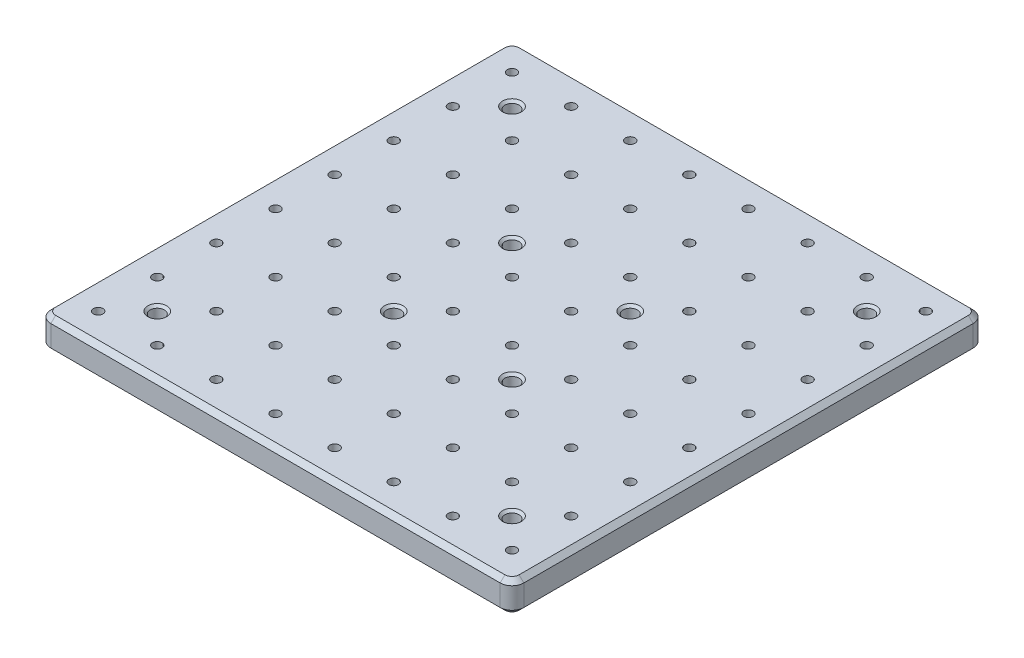
SolidWorks part; units mm, degrees
material "1023 碳钢板 (SS)"
ref_plane "前视基准面" through (0, 0, 0) normal (0, 0, 1) x (1, 0, 0)
ref_plane "上视基准面" through (0, 0, 0) normal (0, 1, 0) x (1, 0, 0)
ref_plane "右视基准面" through (0, 0, 0) normal (1, 0, 0) x (0, 0, -1)
sketch "草图1" plane through (0, 0, 0) normal (0, 1, 0) x (1, 0, 0)
  line L0 (0, 0) -> (0, 125.9326) construction
  line L1 (95, 100) -> (-95, 100)
  line L2 (100, 95) -> (100, -95)
  line L3 (95, -100) -> (-95, -100)
  line L4 (-100, 95) -> (-100, -95)
  line L5 (100, 100) -> (-100, -100) construction
  line L6 (100, -100) -> (-100, 100) construction
  line L7 (25, 25) -> (-25, 25) construction
  line L8 (25, 25) -> (25, -25) construction
  line L9 (25, -25) -> (-25, -25) construction
  line L10 (-25, 25) -> (-25, -25) construction
  line L11 (25, 25) -> (-25, -25) construction
  line L12 (25, -25) -> (-25, 25) construction
  line L13 (-37.5, 37.5) -> (-12.5, 37.5) construction
  line L14 (-37.5, 37.5) -> (-37.5, 12.5) construction
  line L15 (-37.5, 12.5) -> (-12.5, 12.5) construction
  line L16 (-12.5, 37.5) -> (-12.5, 12.5) construction
  line L17 (-37.5, 37.5) -> (-12.5, 12.5) construction
  line L18 (-37.5, 12.5) -> (-12.5, 37.5) construction
  line L20 (75, 75) -> (-75, 75) construction
  line L25 (75, 75) -> (75, -75) construction
  line L26 (75, -75) -> (-75, -75) construction
  line L27 (25, 75) -> (-25, 25) construction
  line L28 (25, 25) -> (-25, 75) construction
  line L29 (-37.5, 62.5) -> (-12.5, 87.5) construction
  line L30 (-37.5, 87.5) -> (-12.5, 62.5) construction
  line L31 (-37.5, 87.5) -> (-37.5, 62.5) construction
  line L32 (-37.5, 62.5) -> (-12.5, 62.5) construction
  line L33 (-12.5, 87.5) -> (-12.5, 62.5) construction
  line L34 (-37.5, 87.5) -> (-12.5, 87.5) construction
  line L35 (-75, 75) -> (-75, -75) construction
  line L36 (75, 75) -> (-75, -75) construction
  line L37 (75, -75) -> (-75, 75) construction
  circle A1 centre (-25, 25) radius 3
  circle A2 centre (25, 25) radius 3
  circle A3 centre (-25, -25) radius 3
  circle A4 centre (25, -25) radius 3
  circle A5 centre (-37.5, 37.5) radius 2
  circle A6 centre (-12.5, 37.5) radius 2
  circle A7 centre (-12.5, 12.5) radius 2
  circle A8 centre (-37.5, 12.5) radius 2
  circle A9 centre (37.5, 37.5) radius 2
  circle A10 centre (37.5, 12.5) radius 2
  circle A11 centre (12.5, 12.5) radius 2
  circle A12 centre (12.5, 37.5) radius 2
  circle A13 centre (87.5, 37.5) radius 2
  circle A14 centre (87.5, 12.5) radius 2
  circle A15 centre (62.5, 12.5) radius 2
  circle A16 centre (62.5, 37.5) radius 2
  circle A17 centre (-87.5, 37.5) radius 2
  circle A18 centre (-62.5, 37.5) radius 2
  circle A19 centre (-62.5, 12.5) radius 2
  circle A20 centre (-87.5, 12.5) radius 2
  circle A21 centre (-37.5, 87.5) radius 2
  circle A22 centre (-12.5, 87.5) radius 2
  circle A23 centre (-12.5, 62.5) radius 2
  circle A24 centre (-37.5, 62.5) radius 2
  circle A25 centre (37.5, 87.5) radius 2
  circle A26 centre (37.5, 62.5) radius 2
  circle A27 centre (12.5, 62.5) radius 2
  circle A28 centre (12.5, 87.5) radius 2
  circle A29 centre (87.5, 87.5) radius 2
  circle A30 centre (87.5, 62.5) radius 2
  circle A31 centre (62.5, 62.5) radius 2
  circle A32 centre (62.5, 87.5) radius 2
  circle A33 centre (-87.5, 87.5) radius 2
  circle A34 centre (-62.5, 87.5) radius 2
  circle A35 centre (-62.5, 62.5) radius 2
  circle A36 centre (-87.5, 62.5) radius 2
  circle A37 centre (-37.5, -12.5) radius 2
  circle A38 centre (-12.5, -12.5) radius 2
  circle A39 centre (-12.5, -37.5) radius 2
  circle A40 centre (-37.5, -37.5) radius 2
  circle A41 centre (37.5, -12.5) radius 2
  circle A42 centre (37.5, -37.5) radius 2
  circle A43 centre (12.5, -37.5) radius 2
  circle A44 centre (12.5, -12.5) radius 2
  circle A45 centre (87.5, -12.5) radius 2
  circle A46 centre (87.5, -37.5) radius 2
  circle A47 centre (62.5, -37.5) radius 2
  circle A48 centre (62.5, -12.5) radius 2
  circle A49 centre (-87.5, -12.5) radius 2
  circle A50 centre (-62.5, -12.5) radius 2
  circle A51 centre (-62.5, -37.5) radius 2
  circle A52 centre (-87.5, -37.5) radius 2
  circle A53 centre (-37.5, -62.5) radius 2
  circle A54 centre (-12.5, -62.5) radius 2
  circle A55 centre (-12.5, -87.5) radius 2
  circle A56 centre (-37.5, -87.5) radius 2
  circle A57 centre (37.5, -62.5) radius 2
  circle A58 centre (37.5, -87.5) radius 2
  circle A59 centre (12.5, -87.5) radius 2
  circle A60 centre (12.5, -62.5) radius 2
  circle A61 centre (87.5, -62.5) radius 2
  circle A62 centre (87.5, -87.5) radius 2
  circle A63 centre (62.5, -87.5) radius 2
  circle A64 centre (62.5, -62.5) radius 2
  circle A65 centre (-87.5, -62.5) radius 2
  circle A66 centre (-62.5, -62.5) radius 2
  circle A67 centre (-62.5, -87.5) radius 2
  circle A68 centre (-87.5, -87.5) radius 2
  arc A69 (100, -95) -> (95, -100) centre (95, -95) cw
  arc A70 (95, 100) -> (100, 95) centre (95, 95) cw
  arc A71 (-95, -100) -> (-100, -95) centre (-95, -95) cw
  arc A72 (-95, 100) -> (-100, 95) centre (-95, 95) ccw
  circle A73 centre (-75, 75) radius 3
  circle A74 centre (-75, -75) radius 3
  circle A75 centre (75, 75) radius 3
  circle A76 centre (75, -75) radius 3
  point P0 (0, 0)
  point P6 (0, 0)
  point P15 (-25, 25)
  point P27 (-25, 75)
  point P175 (0, 0)
  dimension "D3" = 6
  dimension "D4" = 4
  dimension "D12" = 5
  dimension "D1" = 200
  dimension "D2" = 50
  dimension "D5" = 12.5
  dimension "D6" = 25
  dimension "D7" = 3
  dimension "D13" = 50
  dimension "D8" = 2
  dimension "D9" = 2
  dimension "D10" = 2
  dimension "D11" = 2
extrude "凸台-拉伸1" add sketch "草图1" along normal blind 13
chamfer "倒角1" distance 2 angle 45 16 edges at (0, 0, -100) (-98.5355, 0, -98.5355) (98.5355, 0, -98.5355) (-100, 0, 0) (100, 0, 0) (-98.5355, 0, 98.5355) (98.5355, 0, 98.5355) (0, 0, 100) (0, 13, -100) (-98.5355, 13, -98.5355) (98.5355, 13, -98.5355) (-100, 13, 0) (100, 13, 0) (-98.5355, 13, 98.5355) (98.5355, 13, 98.5355) (0, 13, 100)
chamfer "倒角2" distance 1 angle 45 16 edges at (75, 0, 78) (75, 0, -72) (-75, 0, -72) (-75, 0, 78) (-25, 0, -22) (25, 0, -22) (25, 0, 28) (-25, 0, 28) (75, 13, 78) (75, 13, -72) (25, 13, 28) (25, 13, -22) (-75, 13, 78) (-25, 13, 28) (-25, 13, -22) (-75, 13, -72)
